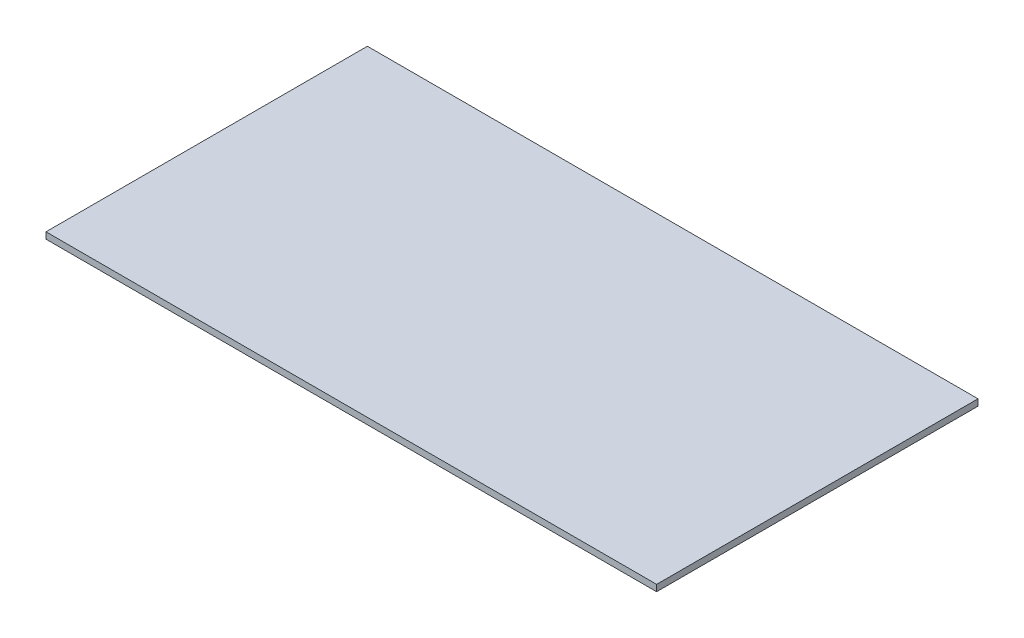
SolidWorks part; units mm, degrees
ref_plane "Front Plane" through (0, 0, 0) normal (0, 0, 1) x (1, 0, 0)
ref_plane "Top Plane" through (0, 0, 0) normal (0, 1, 0) x (1, 0, 0)
ref_plane "Right Plane" through (0, 0, 0) normal (1, 0, 0) x (0, 0, -1)
sketch "Sketch1" plane through (0, 0, 0) normal (0, 1, 0) x (1, 0, 0)
  line L1 (-47.5, 25) -> (47.5, 25)
  line L2 (-47.5, 25) -> (-47.5, -25)
  line L3 (-47.5, -25) -> (47.5, -25)
  line L4 (47.5, 25) -> (47.5, -25)
  line L5 (-47.5, 25) -> (47.5, -25) construction
  line L6 (-47.5, -25) -> (47.5, 25) construction
  point P0 (0, 0)
  dimension "D1" = 95
  dimension "D2" = 50
extrude "Boss-Extrude1" add sketch "Sketch1" along normal mid plane 1
